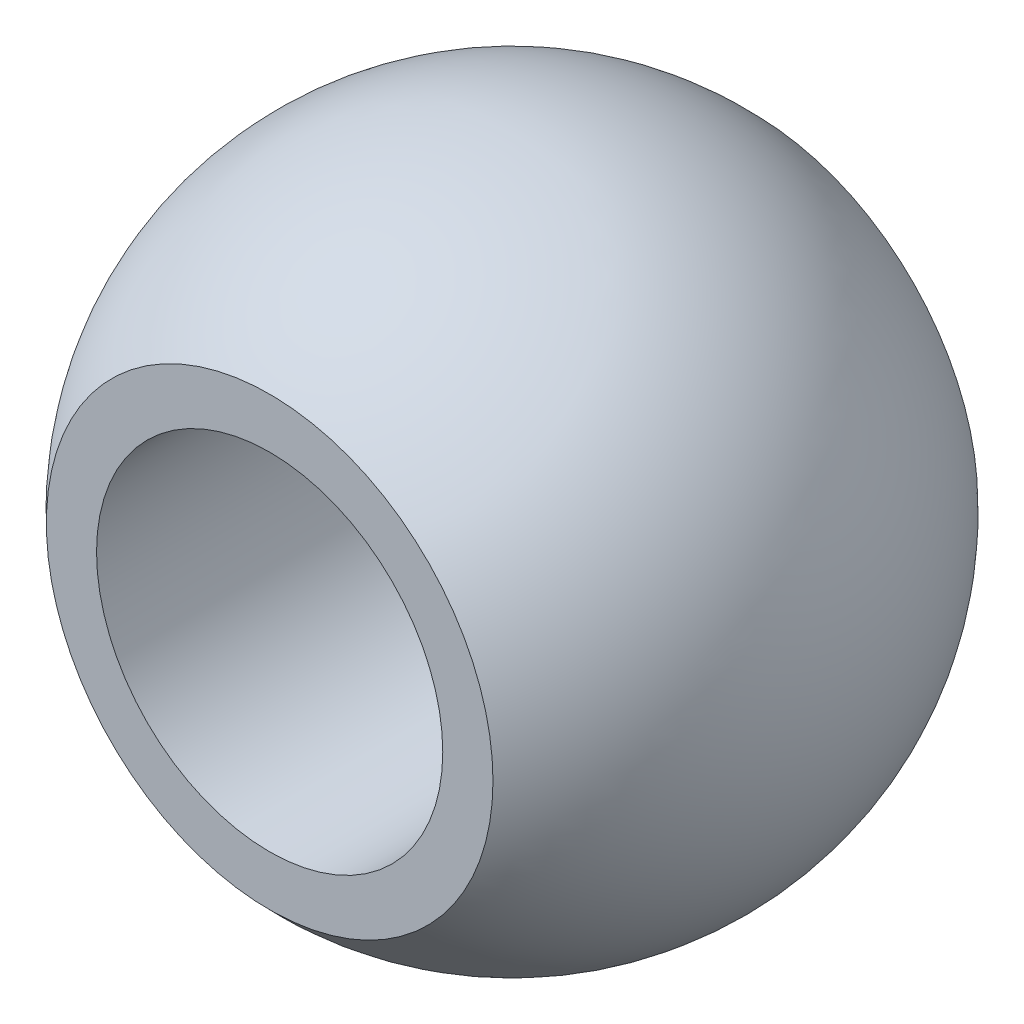
SolidWorks part; units mm, degrees
material "Alloy Steel"
ref_plane "Front Plane" through (0, 0, 0) normal (0, 0, 1) x (1, 0, 0)
ref_plane "Top Plane" through (0, 0, 0) normal (0, 1, 0) x (1, 0, 0)
ref_plane "Right Plane" through (0, 0, 0) normal (1, 0, 0) x (0, 0, -1)
sketch "Sketch1" plane through (0, 0, 0) normal (1, 0, 0) x (0, 0, -1)
  line L0 (-4.6352, 0) -> (49995.3648, 0) construction
  line L1 (0, 9.5185) -> (0, -9.5185) construction
  line L2 (-7, -6.45) -> (7, -6.45) construction
  line L3 (7, -6.45) -> (7, 6.45) construction
  line L7 (-7, -6.45) -> (-7, -5)
  line L8 (-7, -5) -> (7, -5)
  line L9 (7, -5) -> (7, -6.45)
  circle A0 centre (0, 0) radius 9.5185 construction
  arc A1 (7, -6.45) -> (-7, -6.45) centre (0, 0) cw
  dimension "D1" = 14
  dimension "D2" = 12.9
  dimension "D3" = 10
revolve "Revolve1" add sketch "Sketch1" angle 360 about L0
